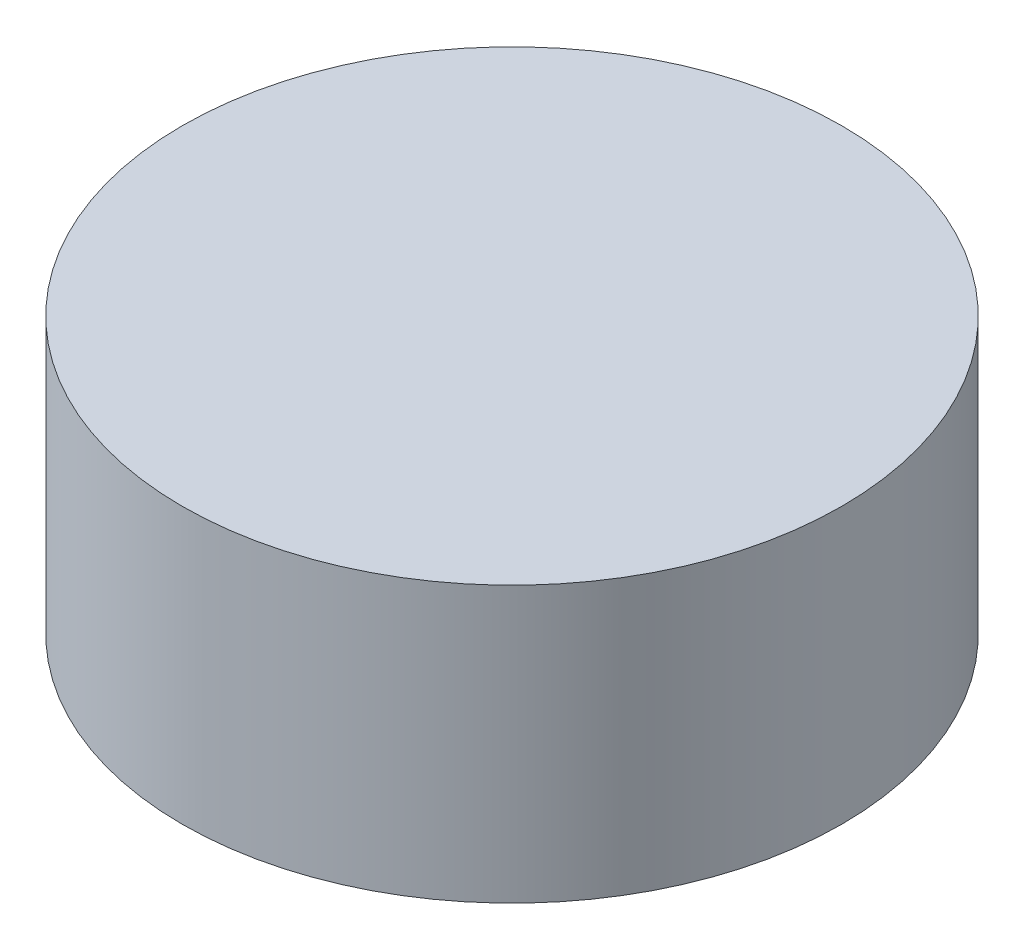
SolidWorks part; units mm, degrees
ref_plane "Ebene vorne" through (0, 0, 0) normal (0, 0, 1) x (1, 0, 0)
ref_plane "Ebene oben" through (0, 0, 0) normal (0, 1, 0) x (1, 0, 0)
ref_plane "Ebene rechts" through (0, 0, 0) normal (1, 0, 0) x (0, 0, -1)
sketch "Skizze2" plane through (0, 0, 0) normal (0, 1, 0) x (1, 0, 0)
  circle A0 centre (0, 0) radius 23.9466
extrude "Aufsatz-Linear austragen1" add sketch "Skizze2" along normal mid plane 20
